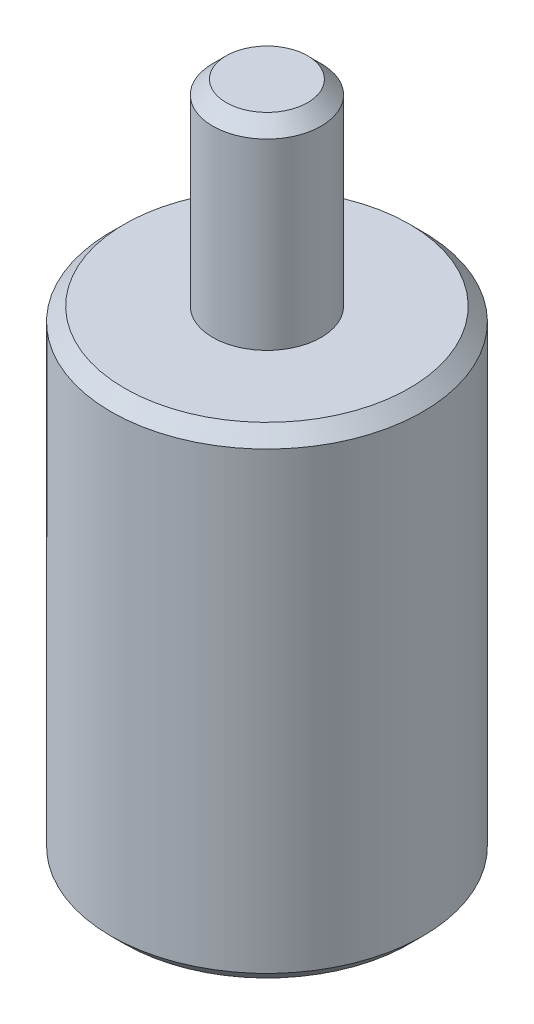
SolidWorks part; units mm, degrees
ref_plane "Front Plane" through (0, 0, 0) normal (0, 0, 1) x (1, 0, 0)
ref_plane "Top Plane" through (0, 0, 0) normal (0, 1, 0) x (1, 0, 0)
ref_plane "Right Plane" through (0, 0, 0) normal (1, 0, 0) x (0, 0, -1)
sketch "Sketch1" plane through (0, 0, 0) normal (0, 1, 0) x (1, 0, 0)
  circle A0 centre (0, 0) radius 1.15
  dimension "D1" = 2.3
extrude "Boss-Extrude1" add sketch "Sketch1" along normal blind 5
sketch "Sketch2" plane through (0, 5, 0) normal (0, 1, 0) x (1, 0, 0)
  circle A0 centre (0, 0) radius 0.4
  dimension "D1" = 0.8
extrude "Cut-Extrude1" cut sketch "Sketch2" against normal blind 1.45 flip side to cut
chamfer "Chamfer1" distance 0.1 angle 45 2 edges at (0, 3.55, 1.15) (0, 0, 1.15)
chamfer "Chamfer2" distance 0.1 angle 45 1 edges at (0, 5, 0.4)
sketch "Sketch3" plane through (0, 0, 0) normal (0, 0, 1) x (1, 0, 0)
  line L0 (0, 0) -> (0, 0.8)
  line L1 (-1.05, 0) -> (1.05, 0) construction
  line L2 (0, 0.8) -> (0.8, 0)
  line L3 (0.8, 0) -> (0, 0)
  line L4 (0, 5) -> (0, 0) construction
  line L5 (0.3, 5) -> (-0.3, 5) construction
  dimension "D1" = 1.6
  dimension "D2" = 45
revolve "Cut-Revolve1" cut sketch "Sketch3" angle 360 about L4
